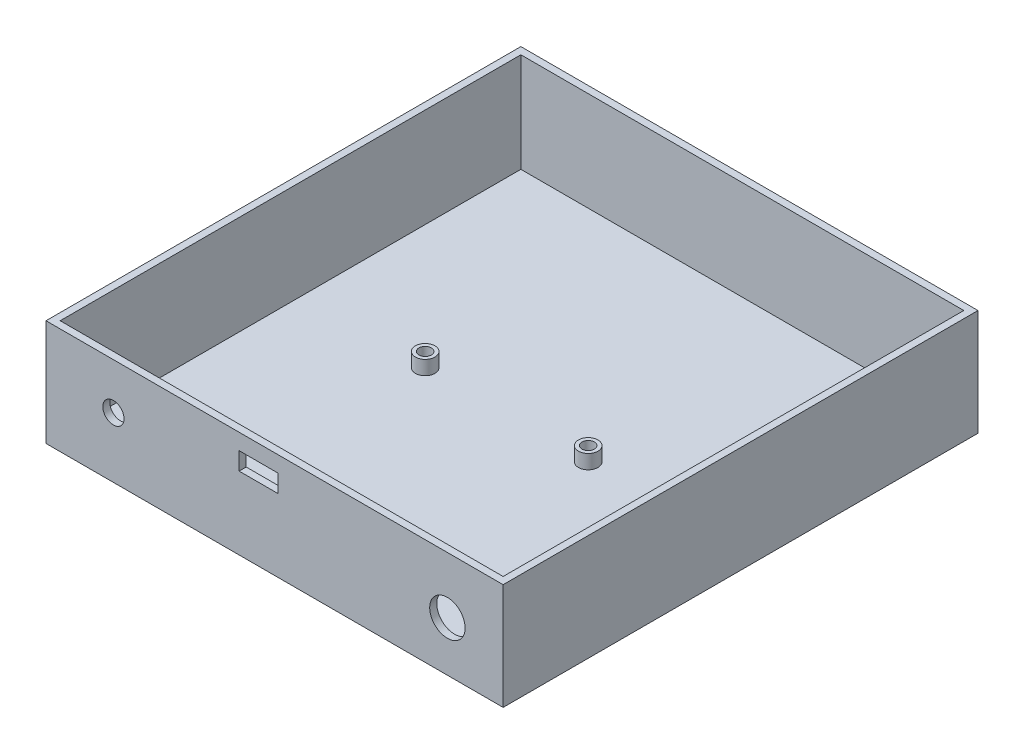
SolidWorks part; units mm, degrees
ref_plane "Front" through (0, 0, 0) normal (0, 0, 1) x (1, 0, 0)
ref_plane "Top" through (0, 0, 0) normal (0, 1, 0) x (1, 0, 0)
ref_plane "Right" through (0, 0, 0) normal (1, 0, 0) x (0, 0, -1)
sketch "Sketch1" plane through (0, 0, 0) normal (0, 1, 0) x (1, 0, 0)
  line L1 (0, 0) -> (125, 0)
  line L2 (0, 0) -> (0, 130)
  line L3 (0, 130) -> (125, 130)
  line L4 (125, 0) -> (125, 130)
  line L5 (0, 0) -> (125, 130) construction
  line L6 (0, 130) -> (125, 0) construction
  point P4 (62.5, 65)
  dimension "D1" = 130
  dimension "D2" = 125
extrude "Boss-Extrude1" add sketch "Sketch1" along normal blind 2
sketch "Sketch2" plane through (0, 0, 0) normal (0, -1, 0) x (1, 0, 0)
  line L8 (-2, 2) -> (-2, -132)
  line L9 (-2, -132) -> (127, -132)
  line L10 (127, -132) -> (127, 2)
  line L11 (127, 2) -> (-2, 2)
  line L12 (-2, 2) -> (-2, -132)
  line L13 (-2, -132) -> (127, -132)
  line L14 (127, -132) -> (127, 2)
  line L15 (127, 2) -> (-2, 2)
  line L16 (0, 0) -> (0, -130)
  line L17 (0, -130) -> (125, -130)
  line L18 (125, -130) -> (125, 0)
  line L19 (125, 0) -> (0, 0)
  line L20 (0, 0) -> (0, -130)
  line L21 (0, -130) -> (125, -130)
  line L22 (125, -130) -> (125, 0)
  line L23 (125, 0) -> (0, 0)
  dimension "D1" = 2
  dimension "D2" = 0
extrude "Boss-Extrude2" add sketch "Sketch2" against normal blind 30
sketch "Sketch3" plane through (0, 2, 0) normal (0, 1, 0) x (1, 0, 0)
  line L0 (33, 0) -> (33, 70) construction
  line L1 (125, 0) -> (0, 0) construction
  line L2 (33, 70) -> (83, 70) construction
  line L3 (83, 70) -> (83, 0) construction
  line L4 (0, 0) -> (125, 0) construction
  line L5 (83, 0) -> (33, 0) construction
  line L6 (0, 130) -> (0, 0) construction
  line L7 (58, 70) -> (58, 0) construction
  line L8 (58, 0) -> (58, 35) construction
  line L9 (33, 35) -> (58, 35) construction
  circle A0 centre (35, 68) radius 2.75
  circle A1 centre (81, 68) radius 2.75
  circle A2 centre (81, 2) radius 2.75
  circle A3 centre (35, 2) radius 2.75
  dimension "D6" = 5.5
  dimension "D1" = 50
  dimension "D2" = 70
  dimension "D3" = 33
  dimension "D4" = 2
  dimension "D5" = 2
extrude "Boss-Extrude3" add sketch "Sketch3" along normal blind 4
sketch "Sketch4" plane through (0, 6, 0) normal (0, 1, 0) x (1, 0, 0)
  circle A0 centre (81, 2) radius 1.75
  circle A1 centre (35, 2) radius 1.75
  circle A2 centre (35, 68) radius 1.75
  circle A3 centre (81, 68) radius 1.75
extrude "Cut-Extrude1" cut sketch "Sketch4" against normal blind 4
ref_plane "Plane1" through (0, 20.5, 0) normal (0, 1, 0) x (1, 0, 0)
sketch "Sketch5" plane through (0, 20.5, 0) normal (0, 1, 0) x (1, 0, 0)
  line L0 (83, 0) -> (33, 0) construction
  line L1 (52.5, 0) -> (63.5, 0)
  line L2 (52.5, 0) -> (52.5, -2)
  line L3 (52.5, -2) -> (63.5, -2)
  line L4 (63.5, 0) -> (63.5, -2)
  line L5 (52.5, 0) -> (63.5, -2) construction
  line L6 (52.5, -2) -> (63.5, 0) construction
  line L7 (127, -2) -> (-2, -2) construction
  line L10 (58, 0) -> (58, -2) construction
  line L11 (0, 0) -> (0, 130) construction
  point P4 (58, -1)
  point P11 (52.5, -1)
  dimension "D1" = 11
  dimension "D2" = 52.5
extrude "Cut-Extrude2" cut sketch "Sketch5" along normal blind 5
sketch "Sketch6" plane through (0, 0, 0) normal (0, 0, -1) x (-1, 0, 0)
  circle A0 centre (-17.0245, 17.0326) radius 3
  circle A1 centre (-111.273, 14.0326) radius 5
extrude "Cut-Extrude3" cut sketch "Sketch6" against normal blind 5
